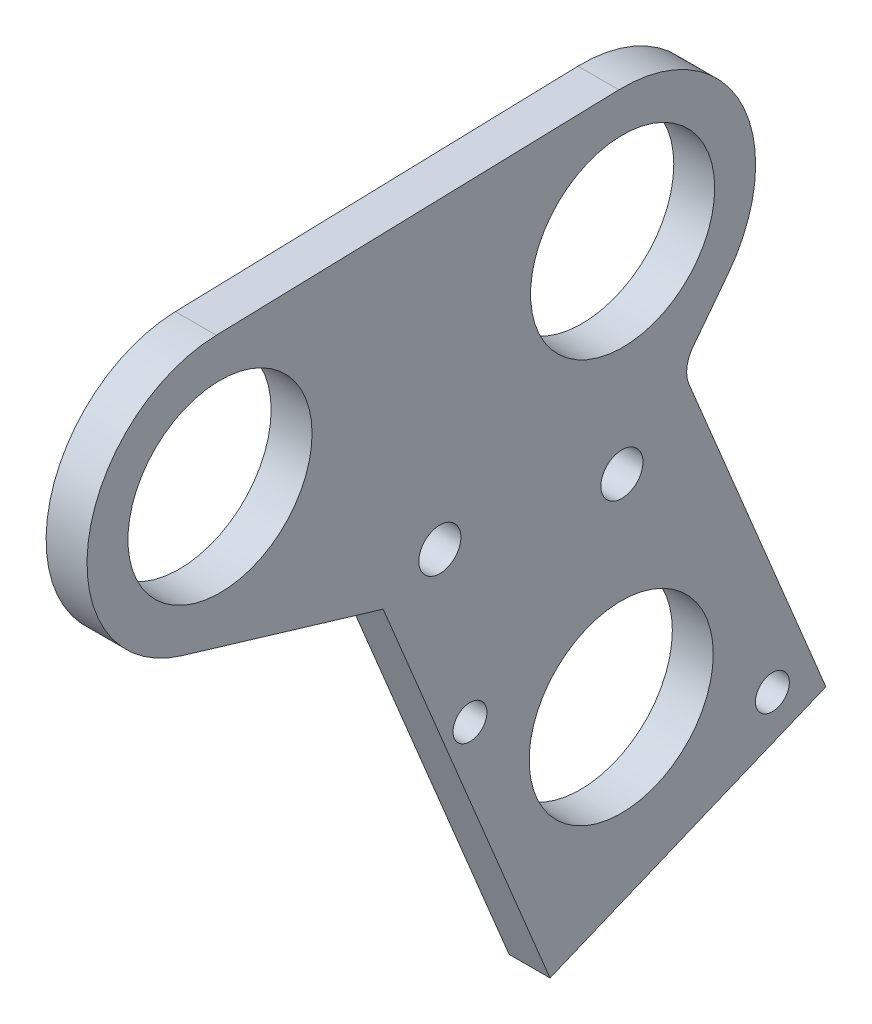
SolidWorks part; units mm, degrees
material "PC High Viscosity"
ref_plane "Front Plane" through (0, 0, 0) normal (0, 0, 1) x (1, 0, 0)
ref_plane "Top Plane" through (0, 0, 0) normal (0, 1, 0) x (1, 0, 0)
ref_plane "Right Plane" through (0, 0, 0) normal (1, 0, 0) x (0, 0, -1)
sketch "Sketch1" plane through (0, 0, 0) normal (1, 0, 0) x (0, 0, -1)
  line L0 (0, 0) -> (32.8446, 0) construction
  line L1 (0, 0) -> (296.112, 106.0517) construction
  line L2 (0, 0) -> (249.1789, 125.492) construction
  line L3 (249.1789, 125.492) -> (296.112, 106.0517) construction
  line L4 (249.1789, 125.492) -> (239.4587, 148.9586) construction
  line L5 (249.1789, 125.492) -> (262.9253, 92.3053) construction
  line L6 (262.9253, 92.3053) -> (296.112, 106.0517) construction
  line L7 (261.6007, 84.8835) -> (235.7041, 147.4033)
  line L8 (235.7041, 147.4033) -> (239.4587, 148.9586) construction
  line L9 (261.6007, 84.8835) -> (304.4086, 102.6151)
  line L10 (304.4086, 102.6151) -> (282.1171, 156.4317)
  line L11 (0, 0) -> (210.3845, 176.5336) construction
  line L12 (241.7905, 198.0574) -> (209.8077, 197.163)
  line L14 (204.4612, 156.7644) -> (235.7041, 147.4033)
  line L15 (210.3845, 176.5336) -> (272.8695, 178.2809) construction
  line L16 (272.6454, 115.7719) -> (272.8695, 178.2809) construction
  line L17 (241.7905, 198.0574) -> (272.2926, 198.9103)
  line L18 (282.1171, 156.4317) -> (289.2423, 165.7176)
  line L19 (235.7041, 147.4033) -> (244.504, 151.0484) construction
  circle A0 centre (296.112, 106.0517) radius 2.6289
  circle A1 centre (249.1789, 125.492) radius 2.6289
  circle A2 centre (272.6454, 115.7719) radius 14.2875
  circle A4 centre (210.3845, 176.5336) radius 14.2875
  arc A5 (209.8077, 197.163) -> (204.4612, 156.7644) centre (210.3845, 176.5336) ccw
  circle A6 centre (210.3845, 176.5336) radius 28.575 construction
  circle A7 centre (0, 0) radius 246.0625 construction
  circle A8 centre (272.8695, 178.2809) radius 14.2875
  arc A9 (289.2423, 165.7176) -> (272.2926, 198.9103) centre (272.8695, 178.2809) ccw
  circle A11 centre (272.7575, 147.0264) radius 3.2639
  circle A12 centre (244.504, 151.0484) radius 3.2639
  dimension "D2" = 5.2578
  dimension "D5" = 5.2578
  dimension "D7" = 28.575
  dimension "D13" = 28.575
  dimension "D14" = 57.15
  dimension "D15" = 20.6375
  dimension "D16" = 492.125
  dimension "D19" = 28.575
  dimension "D20" = 20.6375
  dimension "D22" = 6.5278
  dimension "D23" = 9.525
  dimension "D24" = 6.5278
  dimension "D1" = 19.705
  dimension "D3" = 314.5302
  dimension "D4" = 26.731
  dimension "D6" = 278.9953
  dimension "D8" = 135
  dimension "D9" = 25.4
  dimension "D10" = 4.064
  dimension "D11" = 6.35
  dimension "D12" = 6.35
  dimension "D17" = 40
  dimension "D18" = 62.5094
  dimension "D21" = 120
extrude "Boss-Extrude1" add sketch "Sketch1" along normal blind 6.35
fillet "Fillet1" radius 4.7625 1 edges at (3.175, 156.4317, -282.1171)
